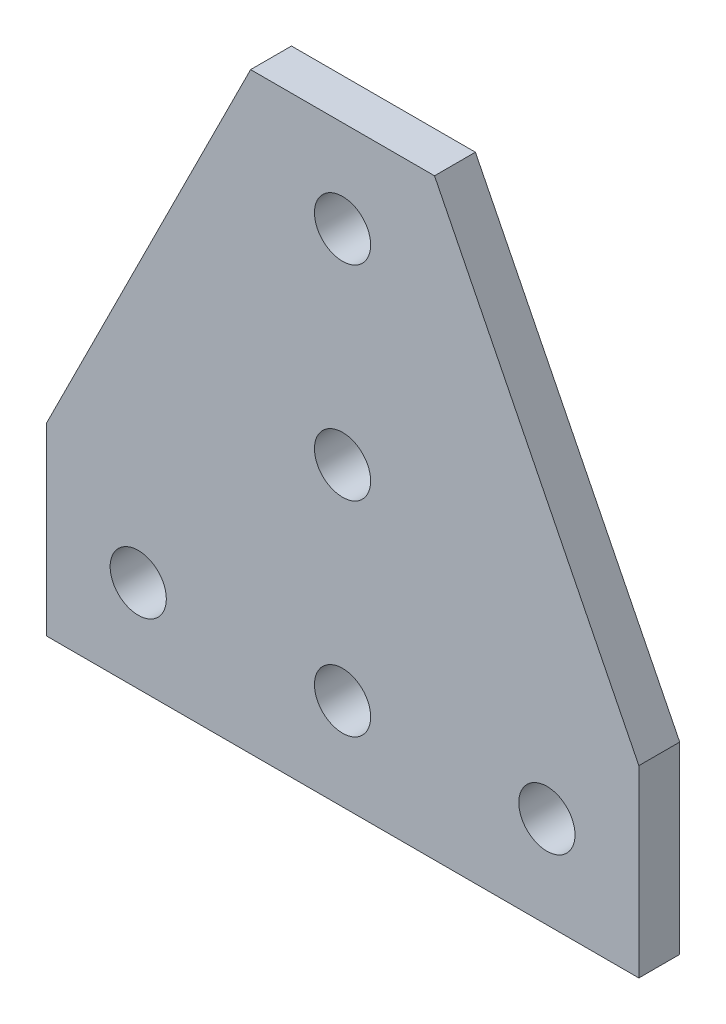
SolidWorks part; units mm, degrees
material "6063-T5"
ref_plane "Front Plane" through (0, 0, 0) normal (0, 0, 1) x (1, 0, 0)
ref_plane "Top Plane" through (0, 0, 0) normal (0, 1, 0) x (1, 0, 0)
ref_plane "Right Plane" through (0, 0, 0) normal (1, 0, 0) x (0, 0, -1)
sketch "Sketch1" plane through (0, 0, 0) normal (0, 0, 1) x (1, 0, 0)
  line L0 (-29, 0) -> (29, 0)
  line L1 (29, 0) -> (29, 18)
  line L2 (29, 18) -> (9, 58)
  line L3 (9, 58) -> (-9, 58)
  line L4 (-9, 58) -> (-29, 18)
  line L5 (-29, 18) -> (-29, 0)
  circle A0 centre (0, 9) radius 2.75
  circle A1 centre (-20, 9) radius 2.75
  circle A2 centre (20, 9) radius 2.75
  circle A3 centre (0, 29) radius 2.75
  circle A4 centre (0, 49) radius 2.75
  point P4 (0, 0)
  point P8 (0, 58)
  dimension "D5" = 9
  dimension "D9" = 5.5
  dimension "D1" = 18
  dimension "D2" = 58
  dimension "D3" = 58
  dimension "D4" = 18
  dimension "D6" = 9
  dimension "D7" = 20
  dimension "D8" = 20
  dimension "D10" = 20
extrude "Boss-Extrude1" add sketch "Sketch1" along normal mid plane 4
